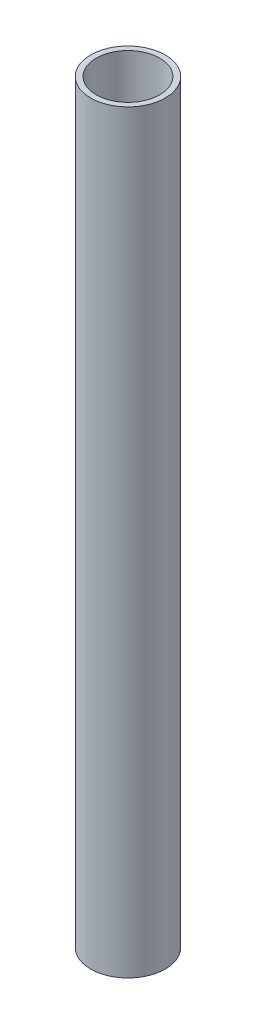
SolidWorks part; units mm, degrees
ref_plane "Front Plane" through (0, 0, 0) normal (0, 0, 1) x (1, 0, 0)
ref_plane "Top Plane" through (0, 0, 0) normal (0, 1, 0) x (1, 0, 0)
ref_plane "Right Plane" through (0, 0, 0) normal (1, 0, 0) x (0, 0, -1)
sketch "Sketch4" plane through (0, 0, 0) normal (1, 0, 0) x (0, 0, -1)
  line L0 (0, 0) -> (0, 273)
  dimension "D1" = 273
sketch "Sketch5" plane through (0, 0, 0) normal (0, 1, 0) x (1, 0, 0)
  circle A0 centre (0, 0) radius 13.5
  circle A1 centre (0, 0) radius 11.5
sweep "Sweep2" add profiles "Sketch5" path "Sketch4"
